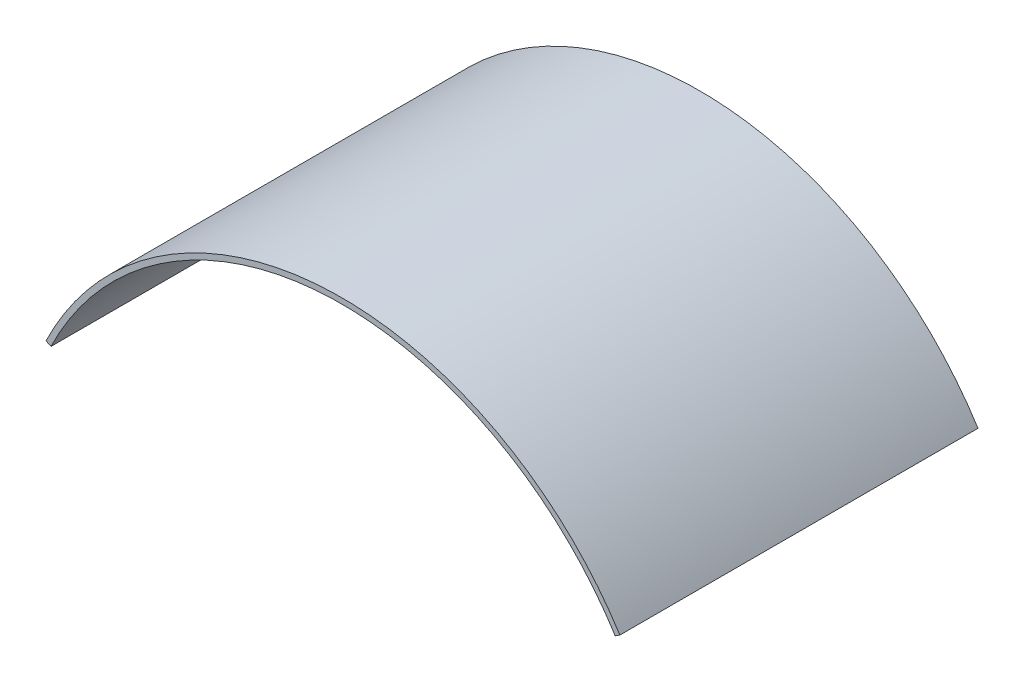
SolidWorks part; units mm, degrees
ref_plane "Front Plane" through (0, 0, 0) normal (0, 0, 1) x (1, 0, 0)
ref_plane "Top Plane" through (0, 0, 0) normal (0, 1, 0) x (1, 0, 0)
ref_plane "Right Plane" through (0, 0, 0) normal (1, 0, 0) x (0, 0, -1)
sketch "Sketch1" plane through (0, 0, 0) normal (0, 0, 1) x (1, 0, 0)
  line L0 (0, 0) -> (1.5743, -0.7642)
  line L1 (181.865, 10.1662) -> (180.3857, 9.2313)
  arc A0 (0, 0) -> (181.865, 10.1662) centre (93.7609, -45.5138) cw
  arc A1 (1.5743, -0.7642) -> (180.3857, 9.2313) centre (93.7609, -45.5138) cw
  arc A2 (0, 0) -> (181.865, 10.1662) centre (93.7609, -45.5138) cw construction
  dimension "D1" = 1.75
extrude "Boss-Extrude1" add sketch "Sketch1" along normal blind 113.5
